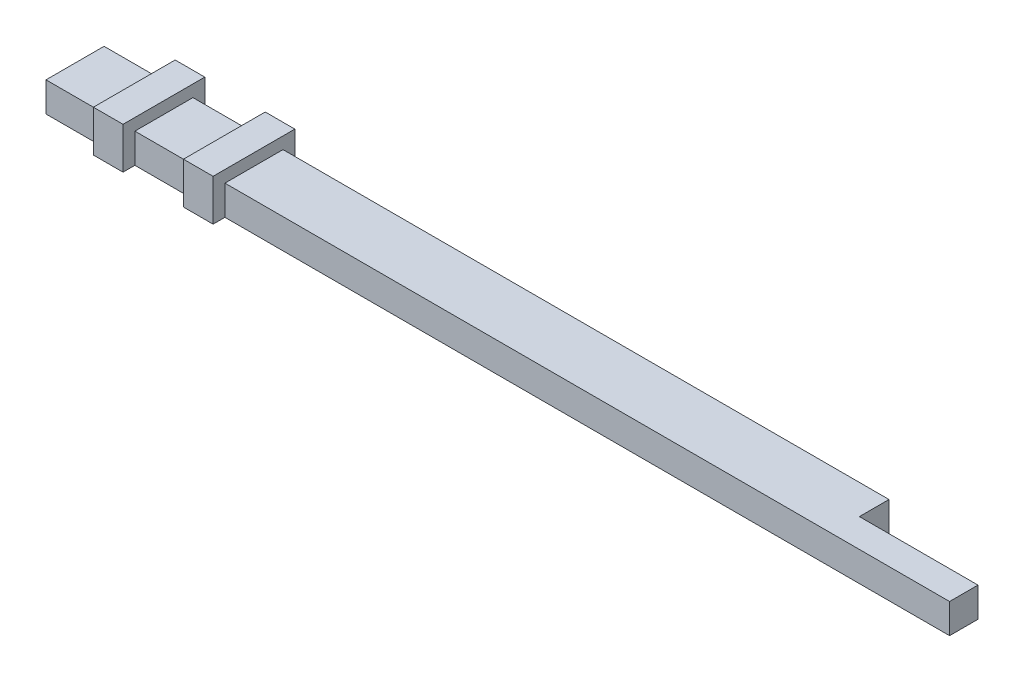
SolidWorks part; units mm, degrees
ref_plane "Front Plane" through (0, 0, 0) normal (0, 0, 1) x (1, 0, 0)
ref_plane "Top Plane" through (0, 0, 0) normal (0, 1, 0) x (1, 0, 0)
ref_plane "Right Plane" through (0, 0, 0) normal (1, 0, 0) x (0, 0, -1)
sketch "Sketch1" plane through (0, 0, 0) normal (0, 1, 0) x (1, 0, 0)
  line L0 (132.4815, 9.8) -> (132.4815, 4.8)
  line L1 (0, 0) -> (142.5, 0)
  line L2 (0, 0) -> (0, 9.8)
  line L3 (0, 9.8) -> (132.4815, 9.8)
  line L5 (142.5, 0) -> (152.5, 0)
  line L7 (142.4815, 4.8) -> (152.5, 4.8)
  line L8 (152.5, 0) -> (152.5, 4.8)
  line L9 (132.4815, 4.8) -> (142.4815, 4.8)
  dimension "D1" = 142.5
  dimension "D2" = 9.8
  dimension "D3" = 10
  dimension "D4" = 10
  dimension "D5" = 4.8
extrude "Boss-Extrude1" add sketch "Sketch1" along normal blind 5
ref_plane "Plane1" through (10, 0, 0) normal (-1, 0, 0) x (0, 0, 1)
sketch "Sketch2" plane through (10, 0, 0) normal (-1, 0, 0) x (0, 0, 1)
  line L0 (-9.8, 5) -> (0, 5) construction
  line L1 (-11.8, 7) -> (2, 7)
  line L2 (-11.8, 7) -> (-11.8, 0)
  line L3 (-11.8, 0) -> (2, 0)
  line L4 (2, 7) -> (2, 0)
  line L5 (-9.8, 0) -> (0, 0) construction
  line L6 (0, 5) -> (0, 0) construction
  line L7 (-9.8, 5) -> (-9.8, 0) construction
  dimension "D1" = 2
  dimension "D2" = 0
  dimension "D3" = 2
  dimension "D4" = 2
extrude "Boss-Extrude2" add sketch "Sketch2" against normal blind 5
ref_plane "Plane2" through (30.2, 0, 0) normal (1, 0, 0) x (0, 0, -1)
sketch "Sketch3" plane through (30.2, 0, 0) normal (1, 0, 0) x (0, 0, -1)
  line L1 (-2, 7) -> (11.8, 7)
  line L2 (-2, 7) -> (-2, 0)
  line L3 (-2, 0) -> (11.8, 0)
  line L4 (11.8, 7) -> (11.8, 0)
extrude "Boss-Extrude3" add sketch "Sketch3" against normal blind 5
